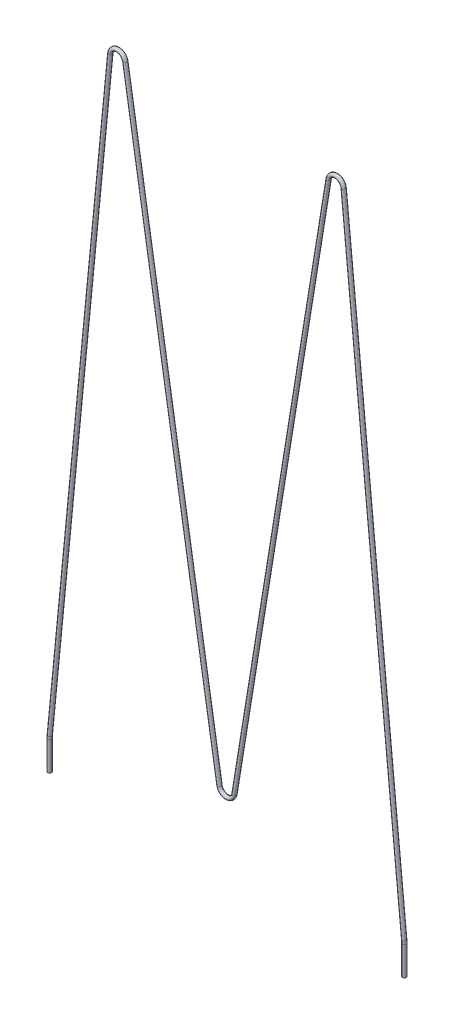
SolidWorks part; units mm, degrees
material "Tungsten"
ref_plane "Front Plane" through (0, 0, 0) normal (0, 0, 1) x (1, 0, 0)
ref_plane "Top Plane" through (0, 0, 0) normal (0, 1, 0) x (1, 0, 0)
ref_plane "Right Plane" through (0, 0, 0) normal (1, 0, 0) x (0, 0, -1)
ref_plane "Plane1" through (0, 12, 0) normal (0, 1, 0) x (-1, 0, 0)
ref_plane "Plane2" through (0, 55, 0) normal (0, 1, 0) x (-1, 0, 0)
sketch "Sketch1" plane through (0, 0, 0) normal (0, 0, 1) x (1, 0, 0)
  line L0 (-11.7, 12) -> (-11.7, 13.9027)
  line L1 (0, -55) -> (0, 55) construction
  line L2 (11.7, 13.9027) -> (11.7, 12)
  line L4 (55, 12) -> (-55, 12) construction
  line L5 (55, 55) -> (-55, 55) construction
  line L6 (-11.6906, 14.0968) -> (-7.6976, 55.0485)
  line L7 (-6.7065, 55.0801) -> (-0.4935, 16.8199)
  line L8 (0.4935, 16.8199) -> (6.7065, 55.0801)
  line L9 (7.6976, 55.0485) -> (11.6906, 14.0968)
  arc A0 (-6.7065, 55.0801) -> (-7.6976, 55.0485) centre (-7.2, 55) ccw
  arc A1 (7.6976, 55.0485) -> (6.7065, 55.0801) centre (7.2, 55) ccw
  arc A2 (-0.4935, 16.8199) -> (0.4935, 16.8199) centre (0, 16.9) ccw
  arc A3 (11.7, 13.9027) -> (11.6906, 14.0968) centre (9.7, 13.9027) ccw
  arc A4 (-11.7, 13.9027) -> (-11.6906, 14.0968) centre (-9.7, 13.9027) cw
  point P23 (-11.7, 14)
  dimension "D4" = 1
  dimension "D5" = 1
  dimension "D8" = 1
  dimension "D10" = 2
  dimension "D1" = 11.7
  dimension "D2" = 11.7
  dimension "D3" = 2
  dimension "D6" = 7.2
  dimension "D7" = 7.2
  dimension "D9" = 4.9
sketch "Sketch2" plane through (0, 12, 0) normal (0, 1, 0) x (-1, 0, 0)
  circle A0 centre (11.7, 0) radius 0.125
  dimension "D1" = 0.25
sweep "Sweep1" add profiles "Sketch2" path "Sketch1"
